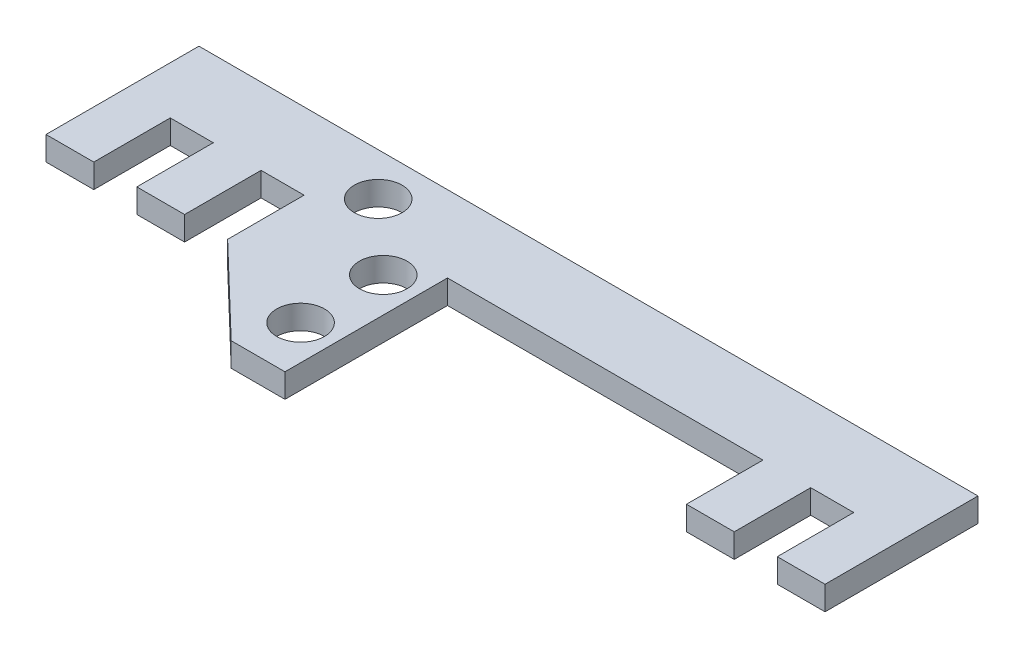
SolidWorks part; units mm, degrees
ref_plane "Front" through (0, 0, 0) normal (0, 0, 1) x (1, 0, 0)
ref_plane "Top" through (0, 0, 0) normal (0, 1, 0) x (1, 0, 0)
ref_plane "Right" through (0, 0, 0) normal (1, 0, 0) x (0, 0, -1)
sketch "Sketch1" plane through (0, 0, 0) normal (0, 1, 0) x (1, 0, 0)
  line L0 (0, 0) -> (0, 6.4)
  line L1 (0, 6.4) -> (32.6, 6.4)
  line L2 (32.6, 6.4) -> (32.6, 0)
  line L3 (32.6, 0) -> (30.6, 0)
  line L4 (30.6, 0) -> (30.6, 3.2)
  line L5 (30.6, 3.2) -> (28.8, 3.2)
  line L6 (28.8, 3.2) -> (28.8, 0)
  line L7 (28.8, 0) -> (26.8, 0)
  line L8 (26.8, 0) -> (26.8, 3.2)
  line L9 (26.8, 3.2) -> (13.6, 3.2)
  line L10 (13.6, 3.2) -> (13.6, -3.6)
  line L11 (13.6, -3.6) -> (11.35, -3.6)
  line L12 (0, 0) -> (2, 0)
  line L13 (2, 0) -> (2, 3.2)
  line L14 (2, 3.2) -> (3.8, 3.2)
  line L15 (3.8, 3.2) -> (3.8, 0)
  line L16 (3.8, 0) -> (5.8, 0)
  line L17 (5.8, 0) -> (5.8, 3.2)
  line L18 (5.8, 3.2) -> (7.6, 3.2)
  line L19 (7.6, 3.2) -> (7.6, 0)
  line L20 (7.6, 0) -> (11.35, -3.6)
extrude "Boss-Extrude1" add sketch "Sketch1" along normal blind 1
sketch "Sketch2" plane through (0, 1, 0) normal (0, 1, 0) x (1, 0, 0)
  circle A0 centre (9.2865, 4.615) radius 1
  circle A1 centre (12.1478, 1.9647) radius 1
  circle A2 centre (12.1478, -1.4941) radius 1
  point P6 (0, 0)
  point P7 (0, 0)
  point P8 (0, 0)
  point P9 (0, 0)
  point P10 (12.1478, 1.9647)
  point P11 (0, 0)
  point P12 (0, 0)
  point P13 (0, 0)
  point P14 (0, 0)
  point P15 (0, 0)
  point P16 (0, 0)
  point P17 (12.1478, -1.0091)
  point P18 (0, 0)
  point P19 (12.5275, -1.4941)
  point P20 (12.1478, -1.4941)
  point P21 (0, 0)
  point P22 (9.4677, 4.6333)
  point P23 (0, 0)
  point P24 (9.2865, 4.615)
extrude "Cut-Extrude1" cut sketch "Sketch2" against normal up to next
